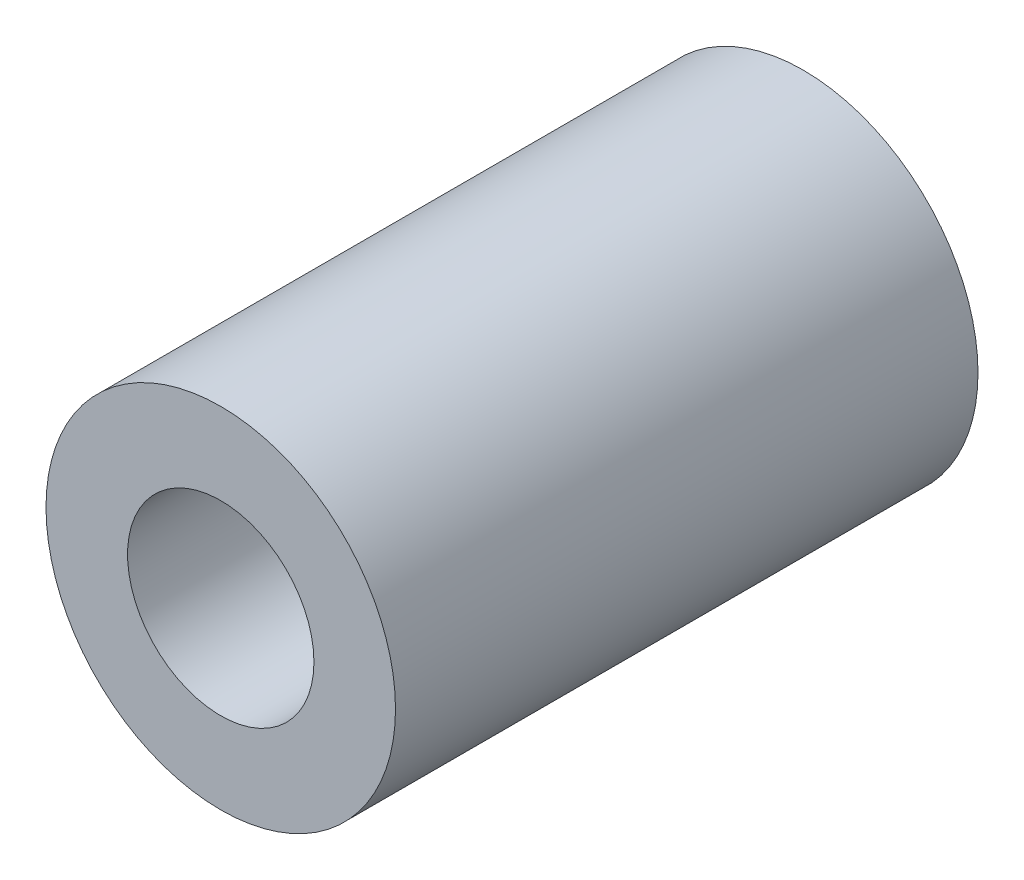
SolidWorks part; units mm, degrees
ref_plane "正面" through (0, 0, 0) normal (0, 0, 1) x (1, 0, 0)
ref_plane "平面" through (0, 0, 0) normal (0, 1, 0) x (1, 0, 0)
ref_plane "右側面" through (0, 0, 0) normal (1, 0, 0) x (0, 0, -1)
sketch "ｽｹｯﾁ1" plane through (0, 0, 0) normal (0, 0, 1) x (1, 0, 0)
  circle A0 centre (0, 0) radius 3
  circle A1 centre (0, 0) radius 1.6
  dimension "D1" = 3.2
  dimension "D2" = 6
extrude "ﾎﾞｽ - 押し出し1" add sketch "ｽｹｯﾁ1" along normal blind 10
